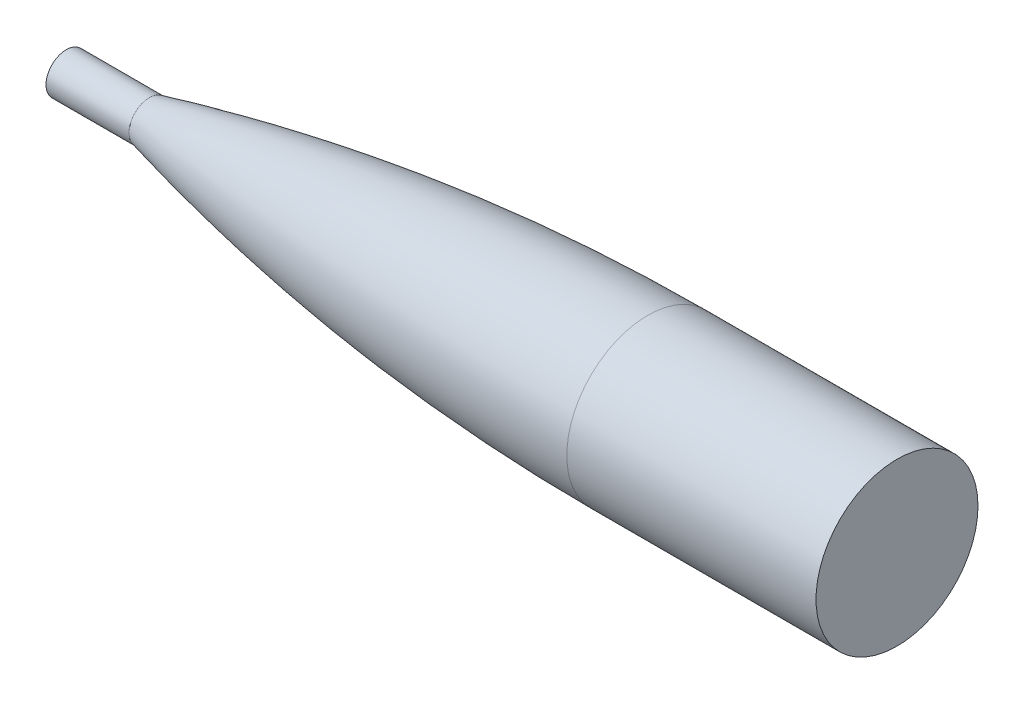
SolidWorks part; units mm, degrees
ref_plane "Front Plane" through (0, 0, 0) normal (0, 0, 1) x (1, 0, 0)
ref_plane "Top Plane" through (0, 0, 0) normal (0, 1, 0) x (1, 0, 0)
ref_plane "Right Plane" through (0, 0, 0) normal (1, 0, 0) x (0, 0, -1)
sketch "Sketch1" plane through (0, 0, 0) normal (0, 1, 0) x (1, 0, 0)
  line L0 (355.6, 50.8) -> (355.6, 1.27)
  line L1 (355.6, 1.27) -> (50.8, 1.27)
  line L2 (50.8, 13.6816) -> (50.8, 1.27)
  spline S0 degree 4 poles (21.2341, 5.9936) (21.856, 6.1634) (23.0998, 6.5019) (25.5843, 7.1746) (28.69, 8.0062) (31.7724, 8.8231) (34.8672, 9.6339) (37.2923, 10.2647) (39.7915, 10.9085) (42.145, 11.5111) (44.7925, 12.1812) (46.8566, 12.7019) (49.9381, 13.4687) (51.3469, 13.8173) (53.9013, 14.445) (55.9043, 14.9331) (57.9182, 15.4203) (59.9692, 15.9131) (62.0056, 16.3987) (64.0459, 16.8817) (66.6196, 17.4865) (69.7274, 18.2096) (73.3707, 19.0464) (77.5504, 19.9917) (82.7791, 21.1557) (97.434, 24.3488) (119.4856, 28.817) (168.0008, 37.516) (219.035, 44.0813) (262.8224, 47.8202) (299.2065, 49.5707) (308.8412, 49.9474) (315.2656, 50.1624) (319.549, 50.2912) (323.8328, 50.4056) (328.117, 50.5056) (332.4014, 50.5911) (336.1391, 50.6531) (339.3296, 50.6971) (341.9732, 50.7276) (344.0698, 50.7484) (346.1633, 50.7657) (348.2725, 50.7795) (350.3447, 50.7899) (352.4057, 50.7968) (355.0352, 50.8005) (356.4848, 50.8002) (359.6537, 50.7954) (361.7791, 50.7854) (364.5032, 50.7703) (366.9275, 50.7502) (369.503, 50.7251) (372.0018, 50.695) (374.5511, 50.6597) (377.0919, 50.6192) (379.6547, 50.5733) (382.2234, 50.522) (384.1523, 50.4796) (385.4374, 50.4496) (386.0799, 50.4342) knots 0 0 0 0 0 0.006986 0.013973 0.027946 0.034806 0.041666 0.048526 0.055386 0.062246 0.069106 0.075966 0.082827 0.088511 0.094195 0.099879 0.105563 0.111247 0.116931 0.122615 0.128299 0.139917 0.151536 0.163154 0.174773 0.19801 0.314194 0.407142 0.709223 0.755697 0.790552 0.802171 0.813789 0.825408 0.837026 0.848645 0.860263 0.871882 0.877566 0.88325 0.888934 0.894618 0.900302 0.905986 0.91167 0.917354 0.924199 0.931044 0.937889 0.944735 0.95158 0.958425 0.96527 0.972115 0.979087 0.986058 0.993029 1 1 1 1 1 construction
  spline S1 degree 4 poles (50.8, 13.6816) (51.2246, 13.7865) (52.0797, 13.9974) (53.9013, 14.445) (55.9043, 14.9331) (57.9182, 15.4203) (59.9692, 15.9131) (62.0056, 16.3987) (64.0459, 16.8817) (66.6196, 17.4865) (69.7274, 18.2096) (73.3707, 19.0464) (77.5504, 19.9917) (82.7791, 21.1557) (97.434, 24.3488) (119.4856, 28.817) (168.0008, 37.516) (219.035, 44.0813) (262.8224, 47.8202) (299.2065, 49.5707) (308.8412, 49.9474) (315.2656, 50.1624) (319.549, 50.2912) (323.8328, 50.4056) (328.117, 50.5056) (332.4014, 50.5911) (336.1391, 50.6531) (339.3296, 50.6971) (341.9732, 50.7276) (344.0698, 50.7484) (346.1633, 50.7657) (348.2725, 50.7795) (350.3447, 50.7899) (352.4057, 50.7968) (354.282, 50.7994) (355.1626, 50.8) (355.6, 50.8) knots 0.082827 0.082827 0.082827 0.082827 0.082827 0.088511 0.094195 0.099879 0.105563 0.111247 0.116931 0.122615 0.128299 0.139917 0.151536 0.163154 0.174773 0.19801 0.314194 0.407142 0.709223 0.755697 0.790552 0.802171 0.813789 0.825408 0.837026 0.848645 0.860263 0.871882 0.877566 0.88325 0.888934 0.894618 0.900302 0.905986 0.91167 0.917354 0.917354 0.917354 0.917354 0.917354
  dimension "D1" = 49.53
  dimension "D2" = 12.4116
revolve "Revolve2" add sketch "Sketch1" angle 360 about L1
ref_plane "Plane1" through (358.14, 0, 0) normal (1, 0, 0) x (0, 0, -1)
sketch "Sketch2" plane through (355.6, 0, 0) normal (1, 0, 0) x (0, 0, -1)
  line L1 (-48.26, 0) -> (50.8, 0) construction
  circle A0 centre (1.27, 0) radius 49.53 construction
  circle A1 centre (1.27, 0) radius 49.53
extrude "Boss-Extrude1" add sketch "Sketch2" along normal blind 152.4
sketch "Sketch3" plane through (50.8, 0, 0) normal (-1, 0, 0) x (0, 0, 1)
  line L0 (-13.6816, 0) -> (11.1416, 0) construction
  circle A0 centre (-1.27, 0) radius 12.4116 construction
  circle A1 centre (-1.27, 0) radius 12.4116
extrude "Boss-Extrude2" add sketch "Sketch3" along normal blind 50.8
